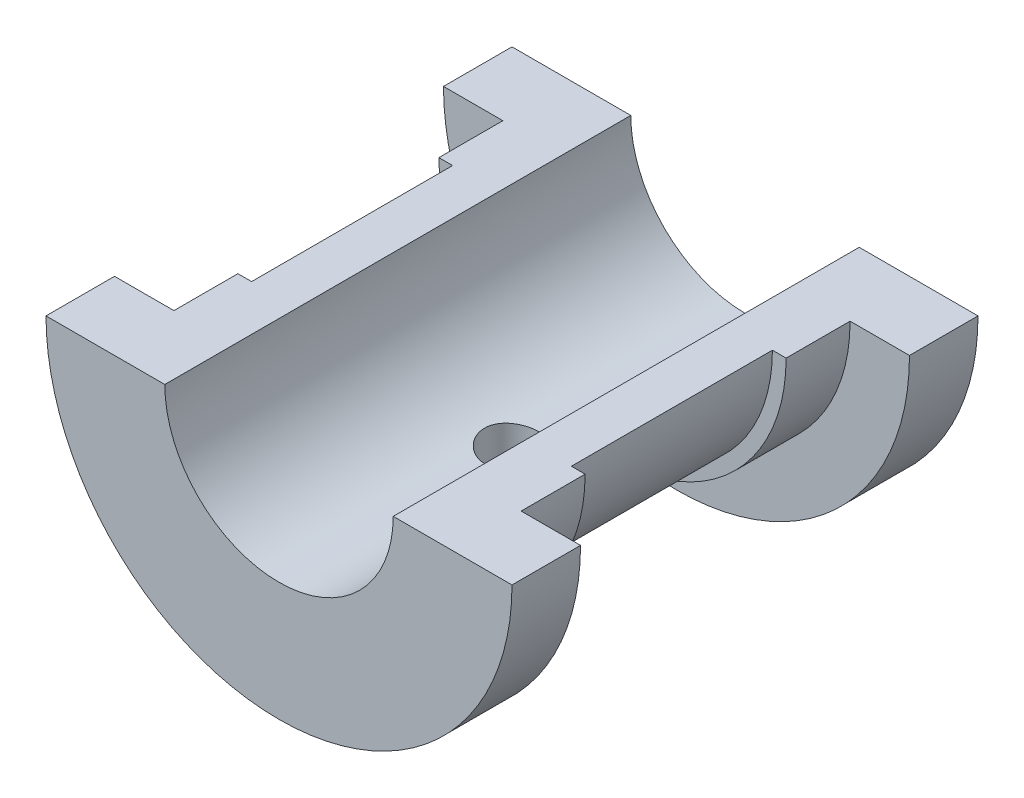
SolidWorks part; units mm, degrees
ref_plane "Front Plane" through (0, 0, 0) normal (0, 0, 1) x (1, 0, 0)
ref_plane "Top Plane" through (0, 0, 0) normal (0, 1, 0) x (1, 0, 0)
ref_plane "Right Plane" through (0, 0, 0) normal (1, 0, 0) x (0, 0, -1)
sketch "Sketch1" plane through (0, 0, 0) normal (0, 1, 0) x (1, 0, 0)
  line L0 (0, 0) -> (0, 67024.655) construction
  line L1 (0, 0) -> (67024.655, 0) construction
  line L2 (-25.5, 25.5) -> (-25.5, 18)
  line L3 (-25.5, 18) -> (-19, 18)
  line L4 (-19, 18) -> (-19, 11)
  line L5 (-19, 11) -> (-17.5, 11)
  line L6 (-17.5, 11) -> (-17.5, -11)
  line L7 (-25.5, 25.5) -> (-12.5, 25.5)
  line L8 (-12.5, 25.5) -> (-12.5, -25.5)
  line L9 (-19, -11) -> (-17.5, -11)
  line L10 (-25.5, -25.5) -> (-12.5, -25.5)
  line L11 (-19, -18) -> (-19, -11)
  line L12 (-25.5, -18) -> (-19, -18)
  line L13 (-25.5, -25.5) -> (-25.5, -18)
  point P15 (-17.5, 0)
  point P16 (-12.5, 0)
  dimension "D1" = 12.5
  dimension "D2" = 17.5
  dimension "D3" = 38
  dimension "D4" = 51
  dimension "D5" = 11
  dimension "D6" = 18
  dimension "D7" = 25.5
revolve "Revolve1" add sketch "Sketch1" angle 180 about L0
ref_plane "Plane1" through (0, -17.5, 0) normal (0, -1, 0) x (-1, 0, 0)
sketch "Sketch2" plane through (0, -17.5, 0) normal (0, -1, 0) x (-1, 0, 0)
  circle A0 centre (0, 0) radius 3
  dimension "D1" = 3
extrude "Cut-Extrude1" cut sketch "Sketch2" against normal through all contours A0
